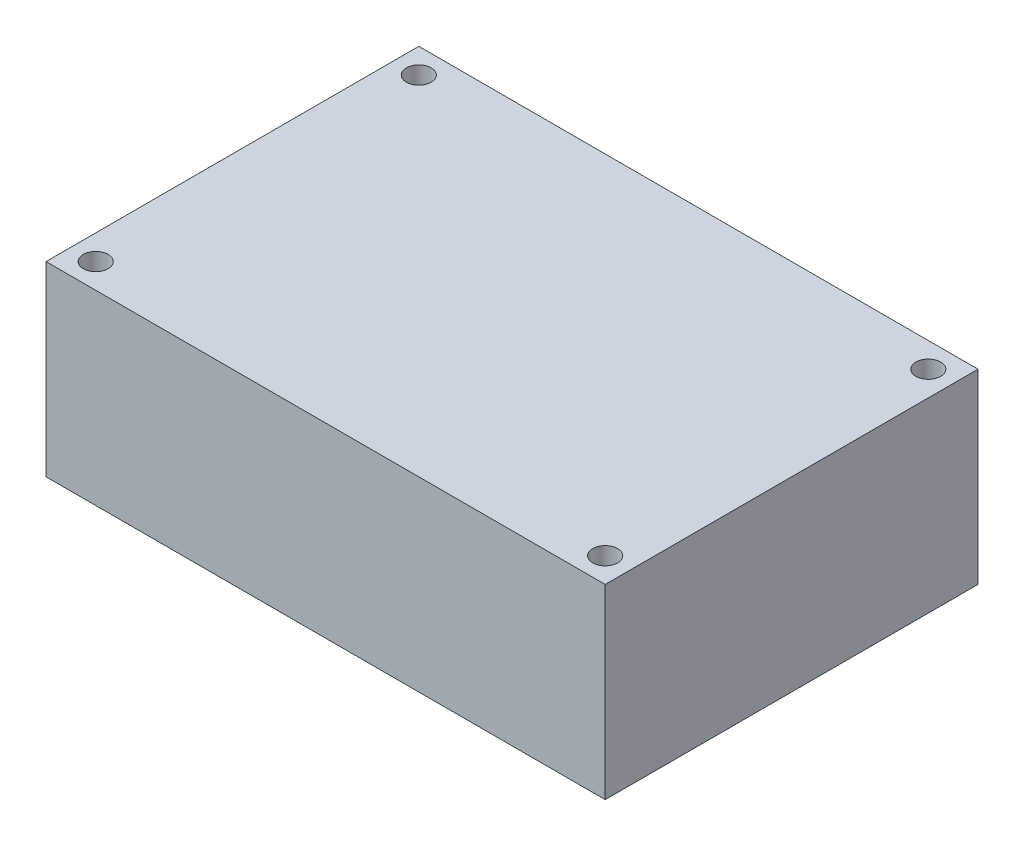
SolidWorks part; units mm, degrees
ref_plane "Front Plane" through (0, 0, 0) normal (0, 0, 1) x (1, 0, 0)
ref_plane "Top Plane" through (0, 0, 0) normal (0, 1, 0) x (1, 0, 0)
ref_plane "Right Plane" through (0, 0, 0) normal (1, 0, 0) x (0, 0, -1)
sketch "Sketch1" plane through (0, 0, 0) normal (0, 1, 0) x (1, 0, 0)
  line L1 (0, 0) -> (-45, 0)
  line L2 (0, 0) -> (0, -30)
  line L3 (0, -30) -> (-45, -30)
  line L4 (-45, 0) -> (-45, -30)
  circle A0 centre (-43, -2) radius 1
  circle A2 centre (-2, -2) radius 1
  circle A4 centre (-43, -28) radius 1
  circle A5 centre (-2, -28) radius 1
  dimension "D1" = 45
  dimension "D2" = 30
extrude "Boss-Extrude1" add sketch "Sketch1" along normal blind 15
